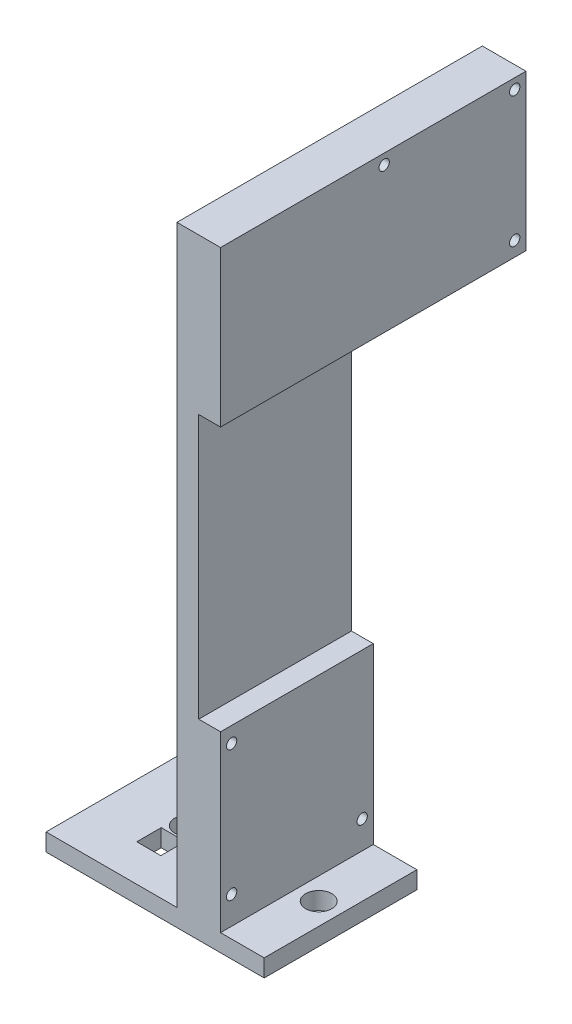
SolidWorks part; units mm, degrees
ref_plane "Front Plane" through (0, 0, 0) normal (0, 0, 1) x (1, 0, 0)
ref_plane "Top Plane" through (0, 0, 0) normal (0, 1, 0) x (1, 0, 0)
ref_plane "Right Plane" through (0, 0, 0) normal (1, 0, 0) x (0, 0, -1)
sketch "Sketch1" plane through (0, 0, 0) normal (0, 1, 0) x (1, 0, 0)
  line L1 (-6.35, -22.225) -> (6.35, -22.225)
  line L2 (-6.35, -22.225) -> (-6.35, 22.225)
  line L3 (-6.35, 22.225) -> (6.35, 22.225)
  line L4 (6.35, -22.225) -> (6.35, 22.225)
  line L5 (-6.35, -22.225) -> (6.35, 22.225) construction
  line L6 (-6.35, 22.225) -> (6.35, -22.225) construction
  point P0 (0, 0)
  dimension "D1" = 12.7
  dimension "D2" = 44.45
extrude "Height extrude" add sketch "Sketch1" along normal blind 172.72
sketch "Sketch2" plane through (6.35, 0, 0) normal (1, 0, 0) x (0, 0, -1)
  line L0 (-22.225, 0) -> (22.225, 0) construction
  circle A0 centre (-19, 8.08) radius 1.5
  circle A1 centre (19, 8.08) radius 1.5
  circle A2 centre (-19, 46.08) radius 1.5
  dimension "D1" = 3
  dimension "D2" = 3
  dimension "D8" = 3
  dimension "D3" = 8.08
  dimension "D4" = 8.08
  dimension "D5" = 19
  dimension "D6" = 19
  dimension "D7" = 38
extrude "Bottom Fan Mount Cuts" cut sketch "Sketch2" against normal through all
sketch "Sketch3" plane through (0, 0, 0) normal (0, -1, 0) x (1, 0, 0)
  line L1 (-44.45, -22.225) -> (19.05, -22.225)
  line L2 (-44.45, -22.225) -> (-44.45, 22.225)
  line L3 (-44.45, 22.225) -> (19.05, 22.225)
  line L4 (19.05, -22.225) -> (19.05, 22.225)
  dimension "D1" = 12.7
  dimension "D2" = 63.5
extrude "Mounting Base Extrude" add sketch "Sketch3" along normal blind 5.08
sketch "Sketch4" plane through (0, 0, 0) normal (0, 1, 0) x (1, 0, 0)
  line L0 (6.35, -22.225) -> (6.35, 22.225) construction
  circle A0 centre (12.7, 0) radius 3.81
  circle A1 centre (-25.4, 0) radius 3.81
  point P6 (6.35, 0)
  dimension "D1" = 7.62
  dimension "D2" = 7.62
  dimension "D3" = 38.1
  dimension "D4" = 6.35
extrude "Mounting Bolt Hole Cut" cut sketch "Sketch4" against normal blind 5.08
sketch "Sketch6" plane through (0, 0, 0) normal (0, 1, 0) x (1, 0, 0)
  line L1 (-28.7593, -11.511) -> (-21.7604, -11.511)
  line L2 (-28.7593, -11.511) -> (-28.7593, -4.3897)
  line L3 (-28.7593, -4.3897) -> (-21.7604, -4.3897)
  line L4 (-21.7604, -11.511) -> (-21.7604, -4.3897)
extrude "Optional Wire Escape Cut" cut sketch "Sketch6" against normal blind 5.08
sketch "Sketch7" plane through (0, 0, -22.225) normal (0, 0, -1) x (-1, 0, 0)
  line L0 (-6.35, 172.72) -> (-6.35, 0) construction
  line L1 (-6.35, 127.4533) -> (6.35, 127.4533)
  line L2 (-6.35, 127.4533) -> (-6.35, 172.72)
  line L3 (-6.35, 172.72) -> (6.35, 172.72)
  line L4 (6.35, 127.4533) -> (6.35, 172.72)
extrude "Boss-Extrude1" add sketch "Sketch7" along normal blind 44.45
sketch "Sketch5" plane through (6.35, 0, 0) normal (1, 0, 0) x (0, 0, -1)
  line L0 (-22.225, 172.72) -> (66.675, 172.72) construction
  circle A0 centre (25.4, 169.72) radius 1.5
  circle A1 centre (63.4, 169.72) radius 1.5
  circle A2 centre (63.4, 131.72) radius 1.5
  dimension "D1" = 3
  dimension "D5" = 3
  dimension "D7" = 3
  dimension "D2" = 3
  dimension "D3" = 25.4
  dimension "D4" = 38
  dimension "D6" = 38
extrude "Top Fan Mount Cuts " cut sketch "Sketch5" against normal through all
sketch "Sketch8" plane through (6.35, 0, 0) normal (1, 0, 0) x (0, 0, -1)
  line L0 (-22.225, 172.72) -> (-22.225, 0) construction
  line L1 (-22.225, 50.6408) -> (22.225, 50.6408)
  line L2 (-22.225, 50.6408) -> (-22.225, 127.4533)
  line L3 (-22.225, 127.4533) -> (22.225, 127.4533)
  line L4 (22.225, 50.6408) -> (22.225, 127.4533)
extrude "Filament no stick cut" cut sketch "Sketch8" against normal blind 6.35
